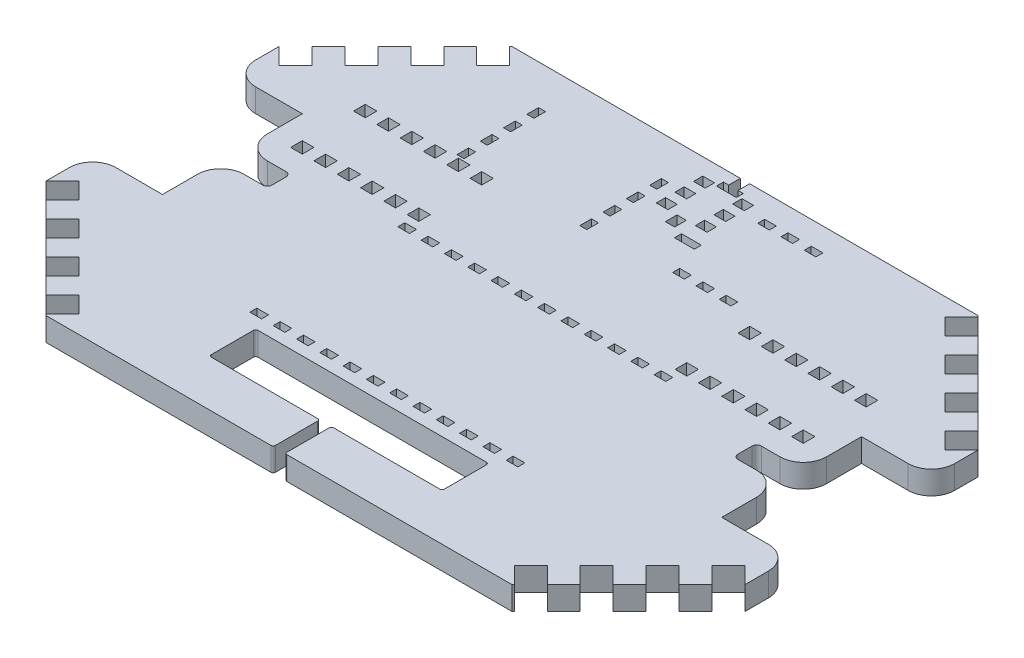
SolidWorks part; units mm, degrees
material "Balsa"
ref_plane "Plan de face" through (0, 0, 0) normal (0, 0, 1) x (1, 0, 0)
ref_plane "Plan de dessus" through (0, 0, 0) normal (0, 1, 0) x (1, 0, 0)
ref_plane "Plan de droite" through (0, 0, 0) normal (1, 0, 0) x (0, 0, -1)
sketch "Esquisse1" plane through (0, 0, 0) normal (0, 1, 0) x (1, 0, 0)
  line L1 (-150, 100) -> (150, 100)
  line L2 (-150, 100) -> (-150, -100)
  line L3 (-150, -100) -> (150, -100)
  line L4 (150, 100) -> (150, -100)
  dimension "D1" = 300
  dimension "D2" = 200
  dimension "D3" = 150
  dimension "D4" = 100
extrude "Boss.-Extru.1" add sketch "Esquisse1" along normal blind 10
sketch "Esquisse2" plane through (0, 10, 0) normal (0, 1, 0) x (1, 0, 0)
  line L0 (-100, 100) -> (-150, 50)
  line L1 (150, 100) -> (-150, 100) construction
  line L2 (-150, 100) -> (-150, -100) construction
  line L3 (-150, 50) -> (-150, 100)
  line L4 (-150, 100) -> (-100, 100)
  line L5 (150, 100) -> (150, 50)
  line L6 (150, -100) -> (150, 100) construction
  line L7 (150, 50) -> (100, 100)
  line L8 (100, 100) -> (150, 100)
  line L9 (150, -100) -> (150, -50)
  line L10 (150, -50) -> (100, -100)
  line L11 (-150, -100) -> (150, -100) construction
  line L12 (100, -100) -> (150, -100)
  line L13 (-100, -100) -> (-150, -100)
  line L14 (-150, -100) -> (-150, -50)
  line L15 (-150, -50) -> (-100, -100)
  dimension "D1" = 50
  dimension "D2" = 50
  dimension "D3" = 50
  dimension "D4" = 50
  dimension "D5" = 50
  dimension "D6" = 50
  dimension "D7" = 50
  dimension "D8" = 50
extrude "Enlèv. mat.-Extru.1" cut sketch "Esquisse2" along direction (0, 1, 0) on the side against the normal up to surface (10 mm away)
sketch "Esquisse12" plane through (0, 10, 0) normal (0, 1, 0) x (1, 0, 0)
  line L0 (-150, 50) -> (-142.9289, 57.0711)
  line L1 (-150, 50) -> (-142.9289, 42.9289)
  line L2 (-142.9289, 57.0711) -> (-135.8579, 50)
  line L3 (-142.9289, 42.9289) -> (-135.8579, 50)
  line L4 (-150, 50) -> (-100, 100) construction
  dimension "D1" = 10
  dimension "D2" = 10
  dimension "D3" = 0
extrude "Enlèv. mat.-Extru.11" cut sketch "Esquisse12" along direction (0, 1, 0) on the side against the normal up to surface (10 mm away)
pattern_linear "Répétition linéaire2" count 4 spacing 20 along (0.7071, 0, -0.7071) of "Enlèv. mat.-Extru.11"
mirror "Symétrie2" about plane through (0, 0, 0) normal (0, 0, 1) of "Répétition linéaire2", "Enlèv. mat.-Extru.11"
mirror "Symétrie3" about plane through (0, 0, 0) normal (1, 0, 0) of "Symétrie2", "Enlèv. mat.-Extru.11", "Répétition linéaire2"
sketch "Esquisse14" plane through (0, 10, 0) normal (0, 1, 0) x (1, 0, 0)
  line L0 (-150, 50) -> (-150, -50) construction
  line L1 (-150, 7.5) -> (-120, 7.5)
  line L2 (-150, 7.5) -> (-150, -7.5)
  line L3 (-150, -7.5) -> (-120, -7.5)
  line L4 (-120, 7.5) -> (-120, -7.5)
  dimension "D1" = 15
  dimension "D2" = 7.5
  dimension "D3" = 30
extrude "Enlèv. mat.-Extru.13" cut sketch "Esquisse14" along direction (0, 1, 0) on the side against the normal up to surface (10 mm away)
sketch "Esquisse15" plane through (0, 10, 0) normal (0, 1, 0) x (1, 0, 0)
  line L0 (-150, -7.5) -> (-120, -7.5) construction
  line L1 (-150, -12.9) -> (-145, -12.9)
  line L2 (-150, -12.9) -> (-150, -17.9)
  line L3 (-150, -17.9) -> (-145, -17.9)
  line L4 (-145, -12.9) -> (-145, -17.9)
  dimension "D1" = 5
  dimension "D2" = 5
  dimension "D3" = 5.4
extrude "Enlèv. mat.-Extru.14" cut sketch "Esquisse15" along direction (0, 1, 0) on the side against the normal up to surface (10 mm away)
pattern_linear "Répétition linéaire3" count 3 spacing 10 along (1, 0, 0) of "Enlèv. mat.-Extru.14"
sketch "Esquisse31" plane through (0, 0, 0) normal (0, -1, 0) x (1, 0, 0)
  line L1 (5.9, -72.8) -> (5.9, -76.8)
  line L2 (5.9, -80.8) -> (5.9, -84.8)
  line L3 (5.9, -88.8) -> (5.9, -92.8)
  line L4 (100, -100) -> (-100, -100) construction
  line L5 (0, -76.3515) -> (0, -99.2722) construction
  line L6 (-5.9, -92.8) -> (-10.9, -92.8)
  line L7 (-5.9, -92.8) -> (-5.9, -88.8)
  line L8 (-5.9, -88.8) -> (-10.9, -88.8)
  line L9 (-10.9, -92.8) -> (-10.9, -88.8)
  line L10 (-10.9, -84.8) -> (-5.9, -84.8)
  line L11 (-10.9, -84.8) -> (-10.9, -80.8)
  line L12 (-10.9, -80.8) -> (-5.9, -80.8)
  line L13 (-5.9, -84.8) -> (-5.9, -80.8)
  line L14 (-5.9, -76.8) -> (-10.9, -76.8)
  line L15 (-5.9, -76.8) -> (-5.9, -72.8)
  line L16 (-5.9, -72.8) -> (-10.9, -72.8)
  line L17 (-10.9, -76.8) -> (-10.9, -72.8)
  line L18 (5.9, -92.8) -> (10.9, -92.8)
  line L19 (10.9, -92.8) -> (10.9, -88.8)
  line L20 (5.9, -88.8) -> (10.9, -88.8)
  line L21 (10.9, -84.8) -> (5.9, -84.8)
  line L22 (10.9, -84.8) -> (10.9, -80.8)
  line L23 (10.9, -80.8) -> (5.9, -80.8)
  line L24 (-2, -72.8) -> (2, -72.8)
  line L25 (5.9, -76.8) -> (10.9, -76.8)
  line L26 (10.9, -76.8) -> (10.9, -72.8)
  line L27 (5.9, -72.8) -> (10.9, -72.8)
  line L28 (-2, -72.8) -> (-2, -67.8)
  line L29 (-2, -67.8) -> (2, -67.8)
  line L30 (2, -72.8) -> (2, -67.8)
  line L31 (-2, -95) -> (2, -95)
  line L32 (-2, -95) -> (-2, -100)
  line L33 (-2, -100) -> (2, -100)
  line L34 (2, -95) -> (2, -100)
  dimension "D2" = 11.8
  dimension "D3" = 4
  dimension "D4" = 3.9
  dimension "D5" = 5
  dimension "D6" = 4
  dimension "D7" = 5
  dimension "D8" = 4
  dimension "D9" = 4
  dimension "D10" = 4
  dimension "D11" = 5
  dimension "D12" = 3.9
  dimension "D13" = 4
  dimension "D14" = 5
  dimension "D15" = 7.2
  dimension "D16" = 5
extrude "Enlèv. mat.-Extru.29" cut sketch "Esquisse31" along direction (0, 1, 0) on the side against the normal up to surface (10 mm away)
sketch "Esquisse32" plane through (0, 0, 0) normal (0, -1, 0) x (1, 0, 0)
  line L0 (150, 50) -> (150, -50) construction
  line L1 (150, -30) -> (120, -30)
  line L2 (150, -30) -> (150, 30)
  line L3 (150, 30) -> (120, 30)
  line L4 (120, -30) -> (120, 30)
  line L6 (0, -34.527) -> (0, 36.2885) construction
  line L7 (-120, -30) -> (-120, 30)
  line L8 (-150, 30) -> (-120, 30)
  line L9 (-150, -30) -> (-150, 30)
  line L10 (-150, -30) -> (-120, -30)
  dimension "D1" = 60
  dimension "D2" = 30
  dimension "D3" = 20
extrude "Enlèv. mat.-Extru.30" cut sketch "Esquisse32" along direction (0, 1, 0) on the side against the normal up to surface (10 mm away)
sketch "Esquisse33" plane through (0, 0, 0) normal (0, -1, 0) x (1, 0, 0)
  line L0 (65, -42) -> (70, -42)
  line L1 (105, -15) -> (110, -15)
  line L2 (105, -15) -> (105, -20)
  line L3 (105, -20) -> (110, -20)
  line L4 (110, -15) -> (110, -20)
  line L5 (150, -30) -> (150, -50) construction
  line L6 (100, -100) -> (2, -100) construction
  line L7 (95, -15) -> (100, -15)
  line L8 (95, -15) -> (95, -20)
  line L9 (95, -20) -> (100, -20)
  line L10 (100, -15) -> (100, -20)
  line L11 (85, -15) -> (90, -15)
  line L12 (85, -15) -> (85, -20)
  line L13 (85, -20) -> (90, -20)
  line L14 (90, -15) -> (90, -20)
  line L15 (75, -15) -> (80, -15)
  line L16 (75, -15) -> (75, -20)
  line L17 (75, -20) -> (80, -20)
  line L18 (80, -15) -> (80, -20)
  line L19 (95, -42) -> (100, -42)
  line L20 (95, -42) -> (95, -47)
  line L21 (95, -47) -> (100, -47)
  line L22 (100, -42) -> (100, -47)
  line L23 (85, -42) -> (90, -42)
  line L24 (85, -42) -> (85, -47)
  line L25 (85, -47) -> (90, -47)
  line L26 (90, -42) -> (90, -47)
  line L27 (75, -42) -> (80, -42)
  line L28 (75, -42) -> (75, -47)
  line L29 (75, -47) -> (80, -47)
  line L30 (80, -42) -> (80, -47)
  line L31 (105, -42) -> (110, -42)
  line L32 (105, -42) -> (105, -47)
  line L33 (105, -47) -> (110, -47)
  line L34 (110, -42) -> (110, -47)
  line L35 (0, -55.2097) -> (0, 81.9109) construction
  line L36 (-110, -42) -> (-110, -47)
  line L37 (-105, -47) -> (-110, -47)
  line L38 (-105, -42) -> (-105, -47)
  line L39 (-105, -42) -> (-110, -42)
  line L40 (-80, -42) -> (-80, -47)
  line L41 (-75, -47) -> (-80, -47)
  line L42 (-75, -42) -> (-75, -47)
  line L43 (-75, -42) -> (-80, -42)
  line L44 (-90, -42) -> (-90, -47)
  line L45 (-85, -47) -> (-90, -47)
  line L46 (-85, -42) -> (-85, -47)
  line L47 (-85, -42) -> (-90, -42)
  line L48 (-100, -42) -> (-100, -47)
  line L49 (-95, -47) -> (-100, -47)
  line L50 (-95, -42) -> (-95, -47)
  line L51 (-95, -42) -> (-100, -42)
  line L52 (-80, -15) -> (-80, -20)
  line L53 (-75, -20) -> (-80, -20)
  line L54 (-75, -15) -> (-75, -20)
  line L55 (-75, -15) -> (-80, -15)
  line L56 (-90, -15) -> (-90, -20)
  line L57 (-85, -20) -> (-90, -20)
  line L58 (-85, -15) -> (-85, -20)
  line L59 (-85, -15) -> (-90, -15)
  line L60 (-100, -15) -> (-100, -20)
  line L61 (-95, -20) -> (-100, -20)
  line L62 (-95, -15) -> (-95, -20)
  line L63 (-95, -15) -> (-100, -15)
  line L64 (-110, -15) -> (-110, -20)
  line L65 (-105, -20) -> (-110, -20)
  line L66 (-105, -15) -> (-105, -20)
  line L67 (-105, -15) -> (-110, -15)
  line L68 (65, -42) -> (65, -47)
  line L69 (65, -47) -> (70, -47)
  line L70 (70, -42) -> (70, -47)
  line L71 (55, -42) -> (60, -42)
  line L72 (55, -42) -> (55, -47)
  line L73 (55, -47) -> (60, -47)
  line L74 (60, -42) -> (60, -47)
  line L75 (65, -15) -> (70, -15)
  line L76 (65, -15) -> (65, -20)
  line L77 (65, -20) -> (70, -20)
  line L78 (70, -15) -> (70, -20)
  line L79 (55, -15) -> (60, -15)
  line L80 (55, -15) -> (55, -20)
  line L81 (55, -20) -> (60, -20)
  line L82 (60, -15) -> (60, -20)
  line L83 (-70, -42) -> (-70, -47)
  line L84 (-65, -47) -> (-70, -47)
  line L85 (-65, -42) -> (-65, -47)
  line L86 (-65, -42) -> (-70, -42)
  line L87 (-70, -15) -> (-70, -20)
  line L88 (-65, -20) -> (-70, -20)
  line L89 (-65, -15) -> (-65, -20)
  line L90 (-65, -15) -> (-70, -15)
  line L91 (-60, -42) -> (-60, -47)
  line L92 (-55, -47) -> (-60, -47)
  line L93 (-55, -42) -> (-55, -47)
  line L94 (-55, -42) -> (-60, -42)
  line L95 (-60, -15) -> (-60, -20)
  line L96 (-55, -20) -> (-60, -20)
  line L97 (-55, -15) -> (-55, -20)
  line L98 (-55, -15) -> (-60, -15)
  dimension "D1" = 5
  dimension "D2" = 5
  dimension "D3" = 40
  dimension "D4" = 80
  dimension "D5" = 4
  dimension "D6" = 2
  dimension "D7" = 3
  dimension "D8" = 3
  dimension "D9" = 3
extrude "Enlèv. mat.-Extru.31" cut sketch "Esquisse33" along direction (0, 1, 0) on the side against the normal up to surface (10 mm away)
sketch "Esquisse34" plane through (0, 0, 0) normal (0, -1, 0) x (1, 0, 0)
  line L0 (-100, 100) -> (100, 100) construction
  line L1 (-50, 80) -> (50, 80)
  line L2 (-50, 80) -> (-50, 60)
  line L3 (-50, 60) -> (50, 60)
  line L4 (50, 80) -> (50, 60)
  line L5 (-150, 30) -> (-150, 50) construction
  line L6 (150, 50) -> (150, 30) construction
  point P8 (150, 40)
  dimension "D1" = 100
  dimension "D2" = 20
  dimension "D3" = 20
  dimension "D4" = 100
  dimension "D5" = 100
extrude "Enlèv. mat.-Extru.33" cut sketch "Esquisse34" along direction (0, 1, 0) on the side against the normal up to surface (10 mm away)
sketch "Esquisse35" plane through (0, 10, 0) normal (0, 1, 0) x (1, 0, 0)
  line L0 (50, -80) -> (-50, -80) construction
  line L1 (-2.5, -80) -> (2.5, -80)
  line L2 (-2.5, -80) -> (-2.5, -100)
  line L3 (-2.5, -100) -> (2.5, -100)
  line L4 (2.5, -80) -> (2.5, -100)
  line L5 (-100, -100) -> (100, -100) construction
  dimension "D1" = 97.5
  dimension "D2" = 97.5
extrude "Enlèv. mat.-Extru.34" cut sketch "Esquisse35" against normal blind 10
fillet "Congé1" radius 1 8 edges at (-50, 5, 80) (-50, 5, 60) (50, 5, 60) (50, 5, 80) (-2.5, 5, 80) (2.5, 5, 80) (-2.5, 5, 100) (2.5, 5, 100)
sketch "Esquisse36" plane through (0, 10, 0) normal (0, 1, 0) x (1, 0, 0)
  line L1 (43.4315, 90) -> (38.4315, 90)
  line L2 (43.4315, 90) -> (43.4315, 87)
  line L3 (43.4315, 87) -> (38.4315, 87)
  line L4 (38.4315, 90) -> (38.4315, 87)
  line L5 (-2, 100) -> (-100, 100) construction
  line L6 (33.4315, 90) -> (28.4315, 90)
  line L7 (33.4315, 90) -> (33.4315, 87)
  line L8 (33.4315, 87) -> (28.4315, 87)
  line L9 (28.4315, 90) -> (28.4315, 87)
  line L10 (23.4315, 90) -> (18.4315, 90)
  line L11 (23.4315, 90) -> (23.4315, 87)
  line L12 (23.4315, 87) -> (18.4315, 87)
  line L13 (18.4315, 90) -> (18.4315, 87)
  line L14 (33.4315, 53.5) -> (28.4315, 53.5)
  line L15 (43.4315, 53.5) -> (38.4315, 53.5)
  line L16 (43.4315, 53.5) -> (43.4315, 50.5)
  line L17 (43.4315, 50.5) -> (38.4315, 50.5)
  line L18 (38.4315, 53.5) -> (38.4315, 50.5)
  line L19 (33.4315, 53.5) -> (33.4315, 50.5)
  line L20 (33.4315, 50.5) -> (28.4315, 50.5)
  line L21 (28.4315, 53.5) -> (28.4315, 50.5)
  line L22 (23.4315, 53.5) -> (18.4315, 53.5)
  line L23 (23.4315, 53.5) -> (23.4315, 50.5)
  line L24 (23.4315, 50.5) -> (18.4315, 50.5)
  line L25 (18.4315, 53.5) -> (18.4315, 50.5)
  dimension "D1" = 3
  dimension "D2" = 5
  dimension "D3" = 10
  dimension "D5" = 33.5
  dimension "D6" = 3
  dimension "D7" = 5
  dimension "D9" = 50
  dimension "D4" = 3
  dimension "D8" = 3
extrude "Enlèv. mat.-Extru.35" cut sketch "Esquisse36" against normal blind 10
sketch "Esquisse37" plane through (0, 10, 0) normal (0, 1, 0) x (1, 0, 0)
  line L1 (14.4574, 63.7901) -> (5.9574, 63.7901)
  line L2 (14.4574, 63.7901) -> (14.4574, 66.7901)
  line L3 (14.4574, 66.7901) -> (5.9574, 66.7901)
  line L4 (5.9574, 63.7901) -> (5.9574, 66.7901)
  dimension "D1" = 3
  dimension "D2" = 8.5
extrude "Enlèv. mat.-Extru.36" cut sketch "Esquisse37" against normal blind 10
sketch "Esquisse39" plane through (0, 10, 0) normal (0, 1, 0) x (1, 0, 0)
  line L0 (2, 95) -> (-2, 95) construction
  line L1 (4.25, 95) -> (-4.25, 95)
  line L2 (4.25, 95) -> (4.25, 92)
  line L3 (4.25, 92) -> (-4.25, 92)
  line L4 (-4.25, 95) -> (-4.25, 92)
  point P4 (0, 95)
  dimension "D1" = 3
  dimension "D2" = 8.5
  dimension "D3" = 4.25
  dimension "D4" = 0
extrude "Enlèv. mat.-Extru.37" cut sketch "Esquisse39" against normal blind 10
sketch "Esquisse40" plane through (0, 10, 0) normal (0, 1, 0) x (1, 0, 0)
  line L0 (-49, -60) -> (49, -60) construction
  line L1 (57.5, -52) -> (52.5, -52)
  line L2 (57.5, -52) -> (57.5, -55)
  line L3 (57.5, -55) -> (52.5, -55)
  line L4 (52.5, -52) -> (52.5, -55)
  line L5 (50, -61) -> (50, -79) construction
  line L6 (47.5, -52) -> (47.5, -55)
  line L7 (47.5, -55) -> (42.5, -55)
  line L8 (42.5, -52) -> (42.5, -55)
  line L9 (47.5, -52) -> (42.5, -52)
  line L10 (37.5, -52) -> (37.5, -55)
  line L11 (37.5, -55) -> (32.5, -55)
  line L12 (32.5, -52) -> (32.5, -55)
  line L13 (37.5, -52) -> (32.5, -52)
  line L14 (27.5, -52) -> (27.5, -55)
  line L15 (27.5, -55) -> (22.5, -55)
  line L16 (22.5, -52) -> (22.5, -55)
  line L17 (27.5, -52) -> (22.5, -52)
  line L18 (17.5, -52) -> (17.5, -55)
  line L19 (17.5, -55) -> (12.5, -55)
  line L20 (12.5, -52) -> (12.5, -55)
  line L21 (17.5, -52) -> (12.5, -52)
  line L22 (7.5, -52) -> (7.5, -55)
  line L23 (7.5, -55) -> (2.5, -55)
  line L24 (2.5, -52) -> (2.5, -55)
  line L25 (7.5, -52) -> (2.5, -52)
  line L26 (-2.5, -52) -> (-2.5, -55)
  line L27 (-2.5, -55) -> (-7.5, -55)
  line L28 (-7.5, -52) -> (-7.5, -55)
  line L29 (-2.5, -52) -> (-7.5, -52)
  line L30 (-12.5, -52) -> (-12.5, -55)
  line L31 (-12.5, -55) -> (-17.5, -55)
  line L32 (-17.5, -52) -> (-17.5, -55)
  line L33 (-12.5, -52) -> (-17.5, -52)
  line L34 (-22.5, -52) -> (-22.5, -55)
  line L35 (-22.5, -55) -> (-27.5, -55)
  line L36 (-27.5, -52) -> (-27.5, -55)
  line L37 (-22.5, -52) -> (-27.5, -52)
  line L38 (-32.5, -52) -> (-32.5, -55)
  line L39 (-32.5, -55) -> (-37.5, -55)
  line L40 (-37.5, -52) -> (-37.5, -55)
  line L41 (-32.5, -52) -> (-37.5, -52)
  line L42 (-42.5, -52) -> (-42.5, -55)
  line L43 (-42.5, -55) -> (-47.5, -55)
  line L44 (-47.5, -52) -> (-47.5, -55)
  line L45 (-42.5, -52) -> (-47.5, -52)
  line L46 (-52.5, -52) -> (-52.5, -55)
  line L47 (-52.5, -55) -> (-57.5, -55)
  line L48 (-57.5, -52) -> (-57.5, -55)
  line L49 (-52.5, -52) -> (-57.5, -52)
  line L50 (61.3005, -21.75) -> (-71.622, -21.75) construction
  line L51 (-52.5, 8.5) -> (-57.5, 8.5)
  line L52 (-57.5, 8.5) -> (-57.5, 11.5)
  line L53 (-52.5, 11.5) -> (-57.5, 11.5)
  line L54 (-52.5, 8.5) -> (-52.5, 11.5)
  line L55 (-42.5, 8.5) -> (-47.5, 8.5)
  line L56 (-47.5, 8.5) -> (-47.5, 11.5)
  line L57 (-42.5, 11.5) -> (-47.5, 11.5)
  line L58 (-42.5, 8.5) -> (-42.5, 11.5)
  line L59 (-32.5, 8.5) -> (-37.5, 8.5)
  line L60 (-37.5, 8.5) -> (-37.5, 11.5)
  line L61 (-32.5, 11.5) -> (-37.5, 11.5)
  line L62 (-32.5, 8.5) -> (-32.5, 11.5)
  line L63 (-22.5, 8.5) -> (-27.5, 8.5)
  line L64 (-27.5, 8.5) -> (-27.5, 11.5)
  line L65 (-22.5, 11.5) -> (-27.5, 11.5)
  line L66 (-22.5, 8.5) -> (-22.5, 11.5)
  line L67 (-12.5, 8.5) -> (-17.5, 8.5)
  line L68 (-17.5, 8.5) -> (-17.5, 11.5)
  line L69 (-12.5, 11.5) -> (-17.5, 11.5)
  line L70 (-12.5, 8.5) -> (-12.5, 11.5)
  line L71 (-2.5, 8.5) -> (-7.5, 8.5)
  line L72 (-7.5, 8.5) -> (-7.5, 11.5)
  line L73 (-2.5, 11.5) -> (-7.5, 11.5)
  line L74 (-2.5, 8.5) -> (-2.5, 11.5)
  line L75 (7.5, 8.5) -> (2.5, 8.5)
  line L76 (2.5, 8.5) -> (2.5, 11.5)
  line L77 (7.5, 11.5) -> (2.5, 11.5)
  line L78 (7.5, 8.5) -> (7.5, 11.5)
  line L79 (17.5, 8.5) -> (12.5, 8.5)
  line L80 (12.5, 8.5) -> (12.5, 11.5)
  line L81 (17.5, 11.5) -> (12.5, 11.5)
  line L82 (17.5, 8.5) -> (17.5, 11.5)
  line L83 (27.5, 8.5) -> (22.5, 8.5)
  line L84 (22.5, 8.5) -> (22.5, 11.5)
  line L85 (27.5, 11.5) -> (22.5, 11.5)
  line L86 (27.5, 8.5) -> (27.5, 11.5)
  line L87 (37.5, 8.5) -> (32.5, 8.5)
  line L88 (32.5, 8.5) -> (32.5, 11.5)
  line L89 (37.5, 11.5) -> (32.5, 11.5)
  line L90 (37.5, 8.5) -> (37.5, 11.5)
  line L91 (47.5, 8.5) -> (42.5, 8.5)
  line L92 (42.5, 8.5) -> (42.5, 11.5)
  line L93 (47.5, 11.5) -> (42.5, 11.5)
  line L94 (47.5, 8.5) -> (47.5, 11.5)
  line L95 (52.5, 8.5) -> (52.5, 11.5)
  line L96 (57.5, 11.5) -> (52.5, 11.5)
  line L97 (57.5, 8.5) -> (57.5, 11.5)
  line L98 (57.5, 8.5) -> (52.5, 8.5)
  dimension "D1" = 3
  dimension "D2" = 5
  dimension "D3" = 5
  dimension "D4" = 7.5
  dimension "D6" = 30.25
  dimension "D5" = 12
extrude "Enlèv. mat.-Extru.39" cut sketch "Esquisse40" against normal blind 10
sketch "Esquisse41" plane through (0, 10, 0) normal (0, 1, 0) x (1, 0, 0)
  line L0 (-10.9, 88.8) -> (-10.9, 92.8) construction
  line L1 (-15.9, 83) -> (-18.9, 83)
  line L2 (-15.9, 83) -> (-15.9, 78)
  line L3 (-15.9, 78) -> (-18.9, 78)
  line L4 (-18.9, 83) -> (-18.9, 78)
  line L5 (-2, 100) -> (-100, 100) construction
  line L6 (-15.9, 68) -> (-18.9, 68)
  line L7 (-15.9, 73) -> (-15.9, 68)
  line L8 (-15.9, 73) -> (-18.9, 73)
  line L9 (-18.9, 73) -> (-18.9, 68)
  line L10 (-15.9, 58) -> (-18.9, 58)
  line L11 (-15.9, 63) -> (-15.9, 58)
  line L12 (-15.9, 63) -> (-18.9, 63)
  line L13 (-18.9, 63) -> (-18.9, 58)
  line L14 (-15.9, 48) -> (-18.9, 48)
  line L15 (-15.9, 53) -> (-15.9, 48)
  line L16 (-15.9, 53) -> (-18.9, 53)
  line L17 (-18.9, 53) -> (-18.9, 48)
  line L18 (-43.75, 44.0546) -> (-43.75, 88.8451) construction
  line L19 (-68.6, 53) -> (-68.6, 48)
  line L20 (-71.6, 53) -> (-68.6, 53)
  line L21 (-71.6, 53) -> (-71.6, 48)
  line L22 (-71.6, 48) -> (-68.6, 48)
  line L23 (-68.6, 63) -> (-68.6, 58)
  line L24 (-71.6, 63) -> (-68.6, 63)
  line L25 (-71.6, 63) -> (-71.6, 58)
  line L26 (-71.6, 58) -> (-68.6, 58)
  line L27 (-68.6, 73) -> (-68.6, 68)
  line L28 (-71.6, 73) -> (-68.6, 73)
  line L29 (-71.6, 73) -> (-71.6, 68)
  line L30 (-71.6, 68) -> (-68.6, 68)
  line L31 (-68.6, 83) -> (-68.6, 78)
  line L32 (-71.6, 78) -> (-68.6, 78)
  line L33 (-71.6, 83) -> (-71.6, 78)
  line L34 (-71.6, 83) -> (-68.6, 83)
  dimension "D1" = 3
  dimension "D2" = 5
  dimension "D3" = 5
  dimension "D4" = 17
  dimension "D6" = 24.85
  dimension "D5" = 4
extrude "Enlèv. mat.-Extru.40" cut sketch "Esquisse41" against normal blind 10
sketch "Esquisse42" plane through (0, 10, 0) normal (0, 1, 0) x (1, 0, 0)
  line L0 (120, -30) -> (120, 30) construction
  line L1 (120, 5) -> (100, 5)
  line L2 (120, 5) -> (120, -5)
  line L3 (120, -5) -> (100, -5)
  line L4 (100, 5) -> (100, -5)
  line L5 (150, -30) -> (120, -30) construction
  line L6 (0, 9.9774) -> (0, -14.8321) construction
  line L7 (-100, 5) -> (-100, -5)
  line L8 (-120, -5) -> (-100, -5)
  line L9 (-120, 5) -> (-120, -5)
  line L10 (-120, 5) -> (-100, 5)
  dimension "D1" = 25
  dimension "D2" = 25
  dimension "D3" = 20
extrude "Enlèv. mat.-Extru.41" cut sketch "Esquisse42" against normal blind 10
fillet "Congé2" radius 10 4 edges at (120, 5, -5) (120, 5, 5) (-120, 5, -5) (-120, 5, 5)
fillet "Congé3" radius 2 4 edges at (-100, 5, -5) (-100, 5, 5) (100, 5, -5) (100, 5, 5)
fillet "Congé4" radius 10 4 edges at (150, 5, -30) (150, 5, 30) (-150, 5, -30) (-150, 5, 30)
